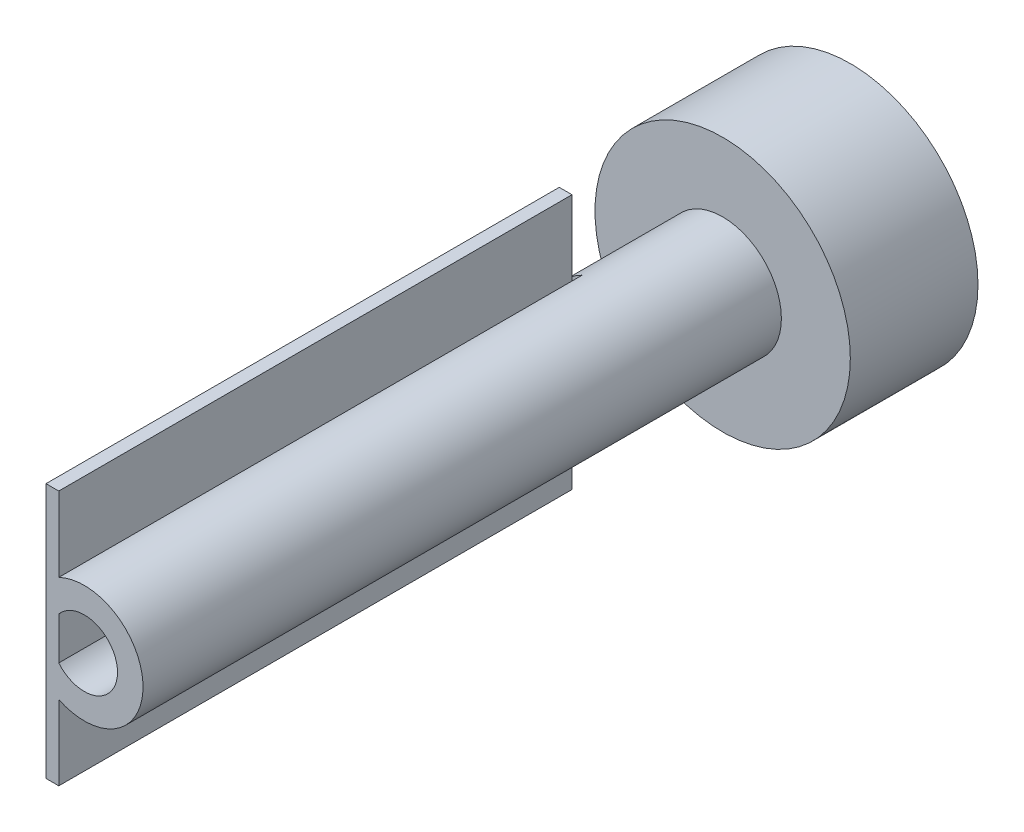
SolidWorks part; units mm, degrees
ref_plane "前视基准面" through (0, 0, 0) normal (0, 0, 1) x (1, 0, 0)
ref_plane "上视基准面" through (0, 0, 0) normal (0, 1, 0) x (1, 0, 0)
ref_plane "右视基准面" through (0, 0, 0) normal (1, 0, 0) x (0, 0, -1)
sketch "草图1" plane through (0, 0, 0) normal (0, 0, 1) x (1, 0, 0)
  circle A0 centre (0, 0) radius 10
  circle A1 centre (0, 0) radius 2.6
  dimension "D1" = 20
  dimension "D2" = 5.2
extrude "凸台-拉伸1" add sketch "草图1" along normal blind 10
sketch "草图2" plane through (0, 0, 10) normal (0, 0, 1) x (1, 0, 0)
  circle A0 centre (0, 0) radius 4.6
  circle A1 centre (0, 0) radius 2.6
  circle A2 centre (0, 0) radius 2.6 construction
  dimension "D1" = 2
extrude "凸台-拉伸2" add sketch "草图2" along normal blind 50
sketch "草图3" plane through (0, 0, 60) normal (0, 0, 1) x (1, 0, 0)
  line L0 (-2, 4.1425) -> (-2, -4.1425)
  circle A0 centre (0, 0) radius 4.6 construction
  arc A1 (-2, 4.1425) -> (-2, -4.1425) centre (0, 0) ccw
  circle A2 centre (0, 0) radius 4.6 construction
  dimension "D1" = 2
extrude "切除-拉伸1" cut sketch "草图3" against normal blind 41
sketch "草图5" plane through (0, 0, 60) normal (0, 0, 1) x (1, 0, 0)
  line L0 (-2, 1.6613) -> (-2, 4.1425) construction
  line L1 (-3, 10) -> (-2, 10)
  line L2 (-3, 10) -> (-3, -10)
  line L3 (-3, -10) -> (-2, -10)
  line L4 (-2, 10) -> (-2, -10)
  point P6 (-3, 0)
  dimension "D1" = 1
  dimension "D2" = 20
extrude "凸台-拉伸3" add sketch "草图5" against normal blind 40.2
